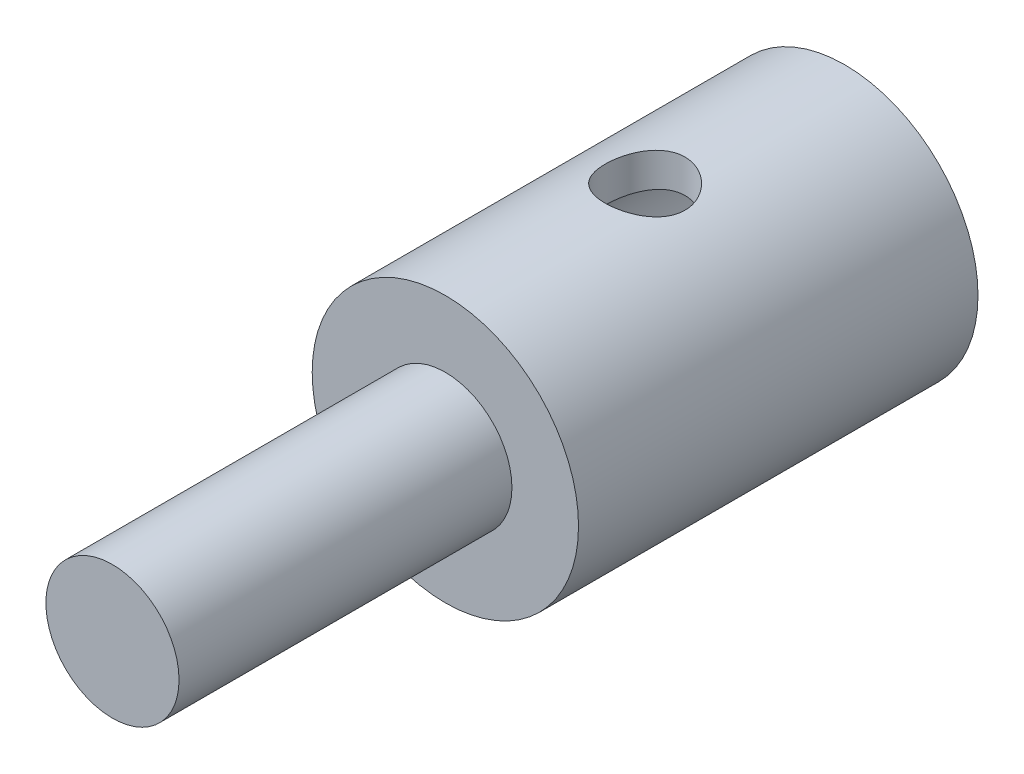
SolidWorks part; units mm, degrees
ref_plane "Plan de face" through (0, 0, 0) normal (0, 0, 1) x (1, 0, 0)
ref_plane "Plan de dessus" through (0, 0, 0) normal (0, 1, 0) x (1, 0, 0)
ref_plane "Plan de droite" through (0, 0, 0) normal (1, 0, 0) x (0, 0, -1)
sketch "Esquisse1" plane through (0, 0, 0) normal (1, 0, 0) x (0, 0, -1)
  line L0 (-5.5, 0) -> (5.5, 0) construction
  line L1 (-5.5, 0) -> (-5.5, 1)
  line L2 (-5.5, 1) -> (-0.5, 1)
  line L3 (-0.5, 1) -> (-0.5, 2)
  line L4 (-0.5, 2) -> (5.5, 2)
  line L5 (5.5, 2) -> (5.5, 1.5)
  line L6 (5.5, 1.5) -> (1.5, 1.5)
  line L7 (1.5, 1.5) -> (1.5, 0)
  line L8 (-5.5, 0) -> (1.5, 0)
  point P6 (0, 0)
  dimension "D1" = 11
  dimension "D2" = 1.5
  dimension "D3" = 6
  dimension "D4" = 2
  dimension "D5" = 1
  dimension "D6" = 4
revolve "Révolution1" add sketch "Esquisse1" angle 360 about L0
sketch "Esquisse2" plane through (0, 0, 0) normal (0, 1, 0) x (1, 0, 0)
  line L0 (-2, 5.5) -> (2, -0.5) construction
  circle A0 centre (0, 2.5) radius 0.6
  dimension "D1" = 1.2
extrude "Enlèv. mat.-Extru.1" cut sketch "Esquisse2" against normal through all and the other way through all
